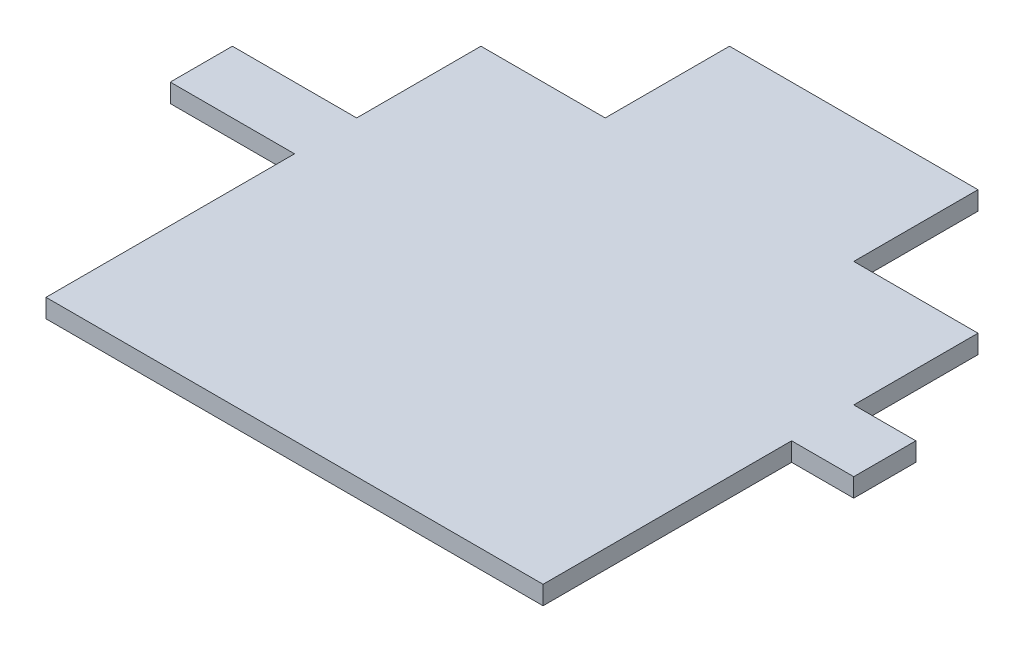
SolidWorks part; units mm, degrees
ref_plane "前视基准面" through (0, 0, 0) normal (0, 0, 1) x (1, 0, 0)
ref_plane "上视基准面" through (0, 0, 0) normal (0, 1, 0) x (1, 0, 0)
ref_plane "右视基准面" through (0, 0, 0) normal (1, 0, 0) x (0, 0, -1)
sketch "草图1" plane through (0, 0, 0) normal (0, 1, 0) x (1, 0, 0)
  line L0 (-38.565, -42.7948) -> (-38.565, -82.7948)
  line L2 (-38.565, -12.7948) -> (-38.565, -32.7948)
  line L3 (-38.565, -82.7948) -> (41.435, -82.7948)
  line L4 (41.435, -12.7948) -> (41.435, -32.7948)
  line L5 (-38.565, -32.7948) -> (-58.565, -32.7948)
  line L7 (-38.565, -42.7948) -> (-58.565, -42.7948)
  line L8 (-58.565, -32.7948) -> (-58.565, -42.7948)
  line L9 (41.435, -32.7948) -> (51.435, -32.7948)
  line L11 (41.435, -42.7948) -> (51.435, -42.7948)
  line L12 (51.435, -32.7948) -> (51.435, -42.7948)
  line L13 (41.435, -42.7948) -> (41.435, -82.7948)
  line L14 (21.435, -12.7948) -> (41.435, -12.7948)
  line L17 (-38.565, -12.7948) -> (-18.565, -12.7948)
  line L20 (-18.565, -12.7948) -> (-18.565, 7.2052)
  line L21 (-18.565, 7.2052) -> (21.435, 7.2052)
  line L22 (21.435, -12.7948) -> (21.435, 7.2052)
  dimension "D1" = 20
  dimension "D2" = 20
  dimension "D3" = 20
  dimension "D4" = 40
  dimension "D5" = 20
  dimension "D6" = 20
  dimension "D7" = 40
  dimension "D8" = 10
  dimension "D9" = 20
  dimension "D10" = 80
extrude "凸台-拉伸1" add sketch "草图1" along normal blind 3
